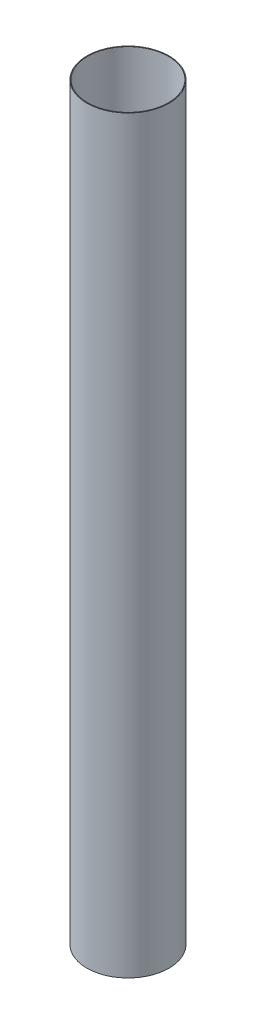
SolidWorks part; units mm, degrees
material "A-Glass Fiber"
ref_plane "Front Plane" through (0, 0, 0) normal (0, 0, 1) x (1, 0, 0)
ref_plane "Top Plane" through (0, 0, 0) normal (0, 1, 0) x (1, 0, 0)
ref_plane "Right Plane" through (0, 0, 0) normal (1, 0, 0) x (0, 0, -1)
sketch "Sketch1" plane through (0, 0, 0) normal (0, 1, 0) x (1, 0, 0)
  circle A0 centre (0, 0) radius 88.9
  circle A1 centre (0, 0) radius 90.4875
  dimension "D1" = 177.8
  dimension "D2" = 180.975
extrude "Boss-Extrude1" add sketch "Sketch1" along normal blind 1651
